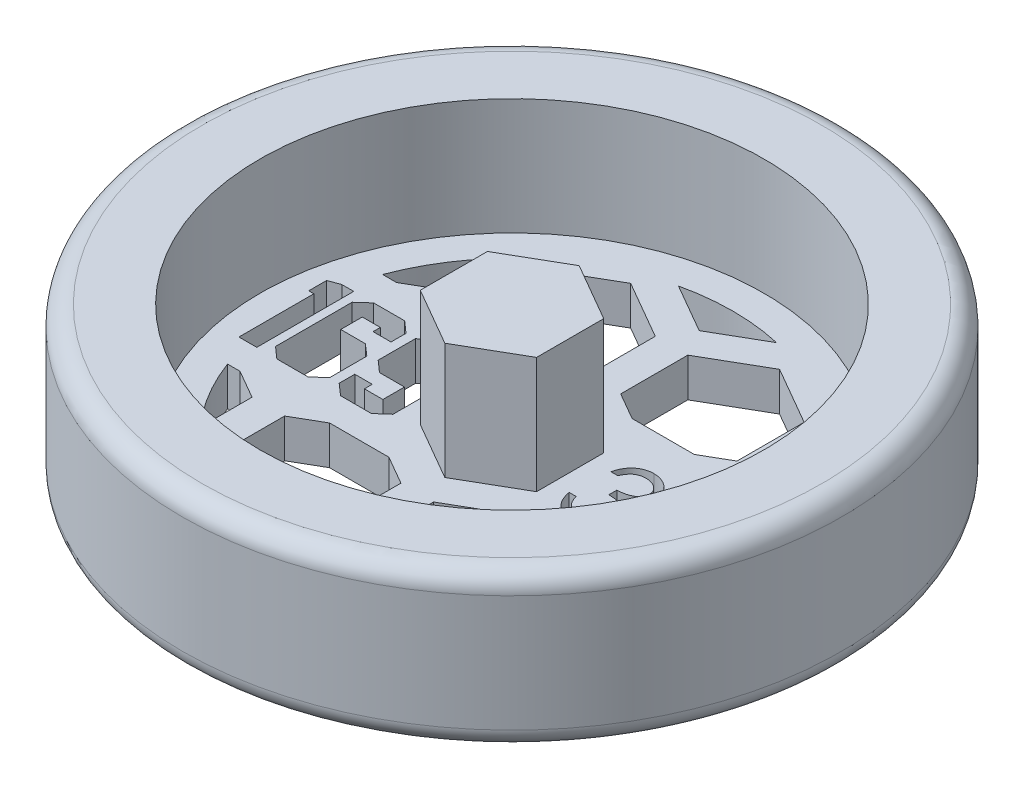
SolidWorks part; units mm, degrees
ref_plane "Front Plane" through (0, 0, 0) normal (0, 0, 1) x (1, 0, 0)
ref_plane "Top Plane" through (0, 0, 0) normal (0, 1, 0) x (1, 0, 0)
ref_plane "Right Plane" through (0, 0, 0) normal (1, 0, 0) x (0, 0, -1)
sketch "Sketch1" plane through (0, 0, 0) normal (0, 0, 1) x (1, 0, 0)
  line L0 (0, 0) -> (25.4, 0)
  line L1 (26.9875, 1.5875) -> (26.9875, 11.1125)
  line L2 (25.4, 12.7) -> (20.6375, 12.7)
  line L3 (20.6375, 12.7) -> (20.6375, 3.175)
  line L4 (20.6375, 3.175) -> (0, 3.175)
  line L5 (0, 3.175) -> (0, 0)
  arc A0 (25.4, 0) -> (26.9875, 1.5875) centre (25.4, 1.5875) ccw
  arc A1 (26.9875, 11.1125) -> (25.4, 12.7) centre (25.4, 11.1125) ccw
  dimension "D5" = 1.5875
  dimension "D1" = 3.175
  dimension "D2" = 6.35
  dimension "D3" = 20.6375
  dimension "D4" = 9.525
revolve "Revolve1" add sketch "Sketch1" angle 360 about L5
sketch "Sketch2" plane through (0, 3.175, 0) normal (0, 1, 0) x (1, 0, 0)
  line L1 (0, 5.4993) -> (-4.7625, 2.7496)
  line L2 (-4.7625, 2.7496) -> (-4.7625, -2.7496)
  line L3 (-4.7625, -2.7496) -> (0, -5.4993)
  line L4 (0, -5.4993) -> (4.7625, -2.7496)
  line L5 (4.7625, -2.7496) -> (4.7625, 2.7496)
  line L6 (4.7625, 2.7496) -> (0, 5.4993)
  circle A0 centre (0, 0) radius 4.7625 construction
  dimension "D1" = 9.525
extrude "Boss-Extrude1" add sketch "Sketch2" along normal blind 9.525
sketch "Sketch3" plane through (0, 3.175, 0) normal (0, 1, 0) x (1, 0, 0)
  line L0 (-4.7625, 0) -> (-20.6375, 0) construction
  line L1 (-4.7625, 2.7496) -> (-4.7625, -2.7496) construction
  line L2 (-4.7625, -3.9688) -> (-20.6375, -3.9688) construction
  line L3 (4.7625, 0) -> (20.6375, 0) construction
  line L4 (4.7625, -2.7496) -> (4.7625, 2.7496) construction
  line L5 (4.7625, -3.175) -> (20.6375, -3.175) construction
  circle A0 centre (0, 0) radius 20.6375 construction
  text T0 "169" font "Jersey M54" height 7.9375
  text T1 "3/8" font "Century Gothic" height 6.35
  dimension "D1" = 3.9688
  dimension "D2" = 3.175
extrude "Cut-Extrude1" cut sketch "Sketch3" against normal through all both and the other way through all
sketch "Sketch4" plane through (0, 3.175, 0) normal (0, 1, 0) x (1, 0, 0)
  line L0 (0, -6.35) -> (0, 6.35)
  line L1 (-16.9469, 6.35) -> (16.9469, 6.35)
  line L2 (-16.9469, -6.35) -> (16.9469, -6.35)
  line L3 (7.4295, -2.7496) -> (12.192, -5.4993)
  line L4 (0, -5.4993) -> (4.7625, -2.7496)
  line L5 (4.7625, -2.7496) -> (4.7625, 2.7496)
  line L6 (4.7625, 2.7496) -> (0, 5.4993)
  line L7 (0, 5.4993) -> (-4.7625, 2.7496)
  line L8 (-4.7625, 2.7496) -> (-4.7625, -2.7496)
  line L9 (-4.7625, -2.7496) -> (0, -5.4993)
  line L10 (6.0325, -15.9479) -> (10.795, -13.1982)
  line L11 (10.795, -13.1982) -> (10.795, -7.699)
  line L12 (10.795, -7.699) -> (6.0325, -4.9493)
  line L13 (6.0325, -4.9493) -> (1.27, -7.699)
  line L14 (1.27, -7.699) -> (1.27, -13.1982)
  line L15 (1.27, -13.1982) -> (6.0325, -15.9479)
  line L16 (7.4295, 2.7496) -> (7.4295, -2.7496)
  line L17 (12.192, 5.4993) -> (7.4295, 2.7496)
  line L18 (16.9545, 2.7496) -> (12.192, 5.4993)
  line L19 (16.9545, -2.7496) -> (16.9545, 2.7496)
  line L20 (12.192, -5.4993) -> (16.9545, -2.7496)
  line L21 (18.2245, -15.9479) -> (22.987, -13.1982)
  line L22 (22.987, -13.1982) -> (22.987, -7.699)
  line L23 (22.987, -7.699) -> (18.2245, -4.9493)
  line L24 (18.2245, -4.9493) -> (13.462, -7.699)
  line L25 (13.462, -7.699) -> (13.462, -13.1982)
  line L26 (13.462, -13.1982) -> (18.2245, -15.9479)
  line L27 (-16.9545, -2.7496) -> (-12.192, -5.4993)
  line L28 (-16.9545, 2.7496) -> (-16.9545, -2.7496)
  line L29 (-12.192, 5.4993) -> (-16.9545, 2.7496)
  line L30 (-7.4295, 2.7496) -> (-12.192, 5.4993)
  line L31 (-7.4295, -2.7496) -> (-7.4295, 2.7496)
  line L32 (-12.192, -5.4993) -> (-7.4295, -2.7496)
  line L33 (-6.1595, -15.9479) -> (-1.397, -13.1982)
  line L34 (-1.397, -13.1982) -> (-1.397, -7.699)
  line L35 (-1.397, -7.699) -> (-6.1595, -4.9493)
  line L36 (-6.1595, -4.9493) -> (-10.922, -7.699)
  line L37 (-10.922, -7.699) -> (-10.922, -13.1982)
  line L38 (-10.922, -13.1982) -> (-6.1595, -15.9479)
  line L39 (-29.1465, -2.7496) -> (-24.384, -5.4993)
  line L40 (-29.1465, 2.7496) -> (-29.1465, -2.7496)
  line L41 (-24.384, 5.4993) -> (-29.1465, 2.7496)
  line L42 (-19.6215, 2.7496) -> (-24.384, 5.4993)
  line L43 (-19.6215, -2.7496) -> (-19.6215, 2.7496)
  line L44 (-24.384, -5.4993) -> (-19.6215, -2.7496)
  line L45 (-18.3515, -15.9479) -> (-13.589, -13.1982)
  line L46 (-13.589, -13.1982) -> (-13.589, -7.699)
  line L47 (-13.589, -7.699) -> (-18.3515, -4.9493)
  line L48 (-18.3515, -4.9493) -> (-23.114, -7.699)
  line L49 (-23.114, -7.699) -> (-23.114, -13.1982)
  line L50 (-23.114, -13.1982) -> (-18.3515, -15.9479)
  line L51 (-4.7625, 18.0784) -> (0, 15.3287)
  line L52 (-4.7625, 23.5776) -> (-4.7625, 18.0784)
  line L53 (0, 26.3273) -> (-4.7625, 23.5776)
  line L54 (4.7625, 23.5776) -> (0, 26.3273)
  line L55 (4.7625, 18.0784) -> (4.7625, 23.5776)
  line L56 (0, 15.3287) -> (4.7625, 18.0784)
  line L57 (6.0325, 4.8801) -> (10.795, 7.6298)
  line L58 (10.795, 7.6298) -> (10.795, 13.129)
  line L59 (10.795, 13.129) -> (6.0325, 15.8787)
  line L60 (6.0325, 15.8787) -> (1.27, 13.129)
  line L61 (1.27, 13.129) -> (1.27, 7.6298)
  line L62 (1.27, 7.6298) -> (6.0325, 4.8801)
  line L63 (-16.9545, 18.0784) -> (-12.192, 15.3287)
  line L64 (-12.192, 15.3287) -> (-7.4295, 18.0784)
  line L65 (-7.4295, 18.0784) -> (-7.4295, 23.5776)
  line L66 (-7.4295, 23.5776) -> (-12.192, 26.3273)
  line L67 (-12.192, 26.3273) -> (-16.9545, 23.5776)
  line L68 (-16.9545, 23.5776) -> (-16.9545, 18.0784)
  line L69 (-29.1465, 18.0784) -> (-24.384, 15.3287)
  line L70 (-24.384, 15.3287) -> (-19.6215, 18.0784)
  line L71 (-19.6215, 18.0784) -> (-19.6215, 23.5776)
  line L72 (-19.6215, 23.5776) -> (-24.384, 26.3273)
  line L73 (-24.384, 26.3273) -> (-29.1465, 23.5776)
  line L74 (-29.1465, 23.5776) -> (-29.1465, 18.0784)
  line L75 (-18.3515, 4.8801) -> (-13.589, 7.6298)
  line L76 (-13.589, 7.6298) -> (-13.589, 13.129)
  line L77 (-13.589, 13.129) -> (-18.3515, 15.8787)
  line L78 (-18.3515, 15.8787) -> (-23.114, 13.129)
  line L79 (-23.114, 13.129) -> (-23.114, 7.6298)
  line L80 (-23.114, 7.6298) -> (-18.3515, 4.8801)
  line L81 (18.2245, 4.8801) -> (22.987, 7.6298)
  line L82 (22.987, 7.6298) -> (22.987, 13.129)
  line L83 (22.987, 13.129) -> (18.2245, 15.8787)
  line L84 (18.2245, 15.8787) -> (13.462, 13.129)
  line L85 (13.462, 13.129) -> (13.462, 7.6298)
  line L86 (13.462, 7.6298) -> (18.2245, 4.8801)
  line L87 (7.4295, 18.0784) -> (12.192, 15.3287)
  line L88 (12.192, 15.3287) -> (16.9545, 18.0784)
  line L89 (16.9545, 18.0784) -> (16.9545, 23.5776)
  line L90 (16.9545, 23.5776) -> (12.192, 26.3273)
  line L91 (12.192, 26.3273) -> (7.4295, 23.5776)
  line L92 (7.4295, 23.5776) -> (7.4295, 18.0784)
  line L93 (-6.1595, 4.8801) -> (-1.397, 7.6298)
  line L94 (-1.397, 7.6298) -> (-1.397, 13.129)
  line L95 (-1.397, 13.129) -> (-6.1595, 15.8787)
  line L96 (-6.1595, 15.8787) -> (-10.922, 13.129)
  line L97 (-10.922, 13.129) -> (-10.922, 7.6298)
  line L98 (-10.922, 7.6298) -> (-6.1595, 4.8801)
  line L99 (-4.7625, -23.5776) -> (0, -26.3273)
  line L100 (-4.7625, -18.0784) -> (-4.7625, -23.5776)
  line L101 (0, -15.3287) -> (-4.7625, -18.0784)
  line L102 (4.7625, -18.0784) -> (0, -15.3287)
  line L103 (4.7625, -23.5776) -> (4.7625, -18.0784)
  line L104 (0, -26.3273) -> (4.7625, -23.5776)
  line L105 (6.0325, -36.7759) -> (10.795, -34.0262)
  line L106 (10.795, -34.0262) -> (10.795, -28.527)
  line L107 (10.795, -28.527) -> (6.0325, -25.7773)
  line L108 (6.0325, -25.7773) -> (1.27, -28.527)
  line L109 (1.27, -28.527) -> (1.27, -34.0262)
  line L110 (1.27, -34.0262) -> (6.0325, -36.7759)
  line L111 (-16.9545, -23.5776) -> (-12.192, -26.3273)
  line L112 (-12.192, -26.3273) -> (-7.4295, -23.5776)
  line L113 (-7.4295, -23.5776) -> (-7.4295, -18.0784)
  line L114 (-7.4295, -18.0784) -> (-12.192, -15.3287)
  line L115 (-12.192, -15.3287) -> (-16.9545, -18.0784)
  line L116 (-16.9545, -18.0784) -> (-16.9545, -23.5776)
  line L117 (-29.1465, -23.5776) -> (-24.384, -26.3273)
  line L118 (-24.384, -26.3273) -> (-19.6215, -23.5776)
  line L119 (-19.6215, -23.5776) -> (-19.6215, -18.0784)
  line L120 (-19.6215, -18.0784) -> (-24.384, -15.3287)
  line L121 (-24.384, -15.3287) -> (-29.1465, -18.0784)
  line L122 (-29.1465, -18.0784) -> (-29.1465, -23.5776)
  line L123 (-18.3515, -36.7759) -> (-13.589, -34.0262)
  line L124 (-13.589, -34.0262) -> (-13.589, -28.527)
  line L125 (-13.589, -28.527) -> (-18.3515, -25.7773)
  line L126 (-18.3515, -25.7773) -> (-23.114, -28.527)
  line L127 (-23.114, -28.527) -> (-23.114, -34.0262)
  line L128 (-23.114, -34.0262) -> (-18.3515, -36.7759)
  line L129 (18.2245, -36.7759) -> (22.987, -34.0262)
  line L130 (22.987, -34.0262) -> (22.987, -28.527)
  line L131 (22.987, -28.527) -> (18.2245, -25.7773)
  line L132 (18.2245, -25.7773) -> (13.462, -28.527)
  line L133 (13.462, -28.527) -> (13.462, -34.0262)
  line L134 (13.462, -34.0262) -> (18.2245, -36.7759)
  line L135 (7.4295, -23.5776) -> (12.192, -26.3273)
  line L136 (12.192, -26.3273) -> (16.9545, -23.5776)
  line L137 (16.9545, -23.5776) -> (16.9545, -18.0784)
  line L138 (16.9545, -18.0784) -> (12.192, -15.3287)
  line L139 (12.192, -15.3287) -> (7.4295, -18.0784)
  line L140 (7.4295, -18.0784) -> (7.4295, -23.5776)
  line L141 (-6.1595, -36.7759) -> (-1.397, -34.0262)
  line L142 (-1.397, -34.0262) -> (-1.397, -28.527)
  line L143 (-1.397, -28.527) -> (-6.1595, -25.7773)
  line L144 (-6.1595, -25.7773) -> (-10.922, -28.527)
  line L145 (-10.922, -28.527) -> (-10.922, -34.0262)
  line L146 (-10.922, -34.0262) -> (-6.1595, -36.7759)
  circle A0 centre (0, 0) radius 18.0975
  circle A1 centre (0, 0) radius 4.7625 construction
  circle A2 centre (6.0325, -10.4486) radius 4.7625 construction
  point P6 (0, 0)
  point P9 (0, 6.35)
  point P12 (0, -6.35)
  dimension "D1" = 36.195
  dimension "D2" = 12.7
  dimension "D3" = 9.525
  dimension "D4" = 2.54
  dimension "D5" = 9.525
  dimension "D6" = 1.27
  dimension "D7" = 2
  dimension "D8" = 3
  dimension "D9" = 2
  dimension "D10" = 2
extrude "Cut-Extrude2" cut sketch "Sketch4" against normal through all both and the other way through all contours L76 A0 L1 L75 | L97 L98 L1 L93 L94 L95 L96 | L56 A0 L51 | L61 L62 L1 L57 L58 L59 L60 | L1 A0 L85 L86 | L14 L15 L10 L11 L12 L2 L13 | L25 A0 L2 L24 | L101 A0 L102 | L37 L38 L33 L34 L35 L2 L36 | L2 A0 L46 L47
